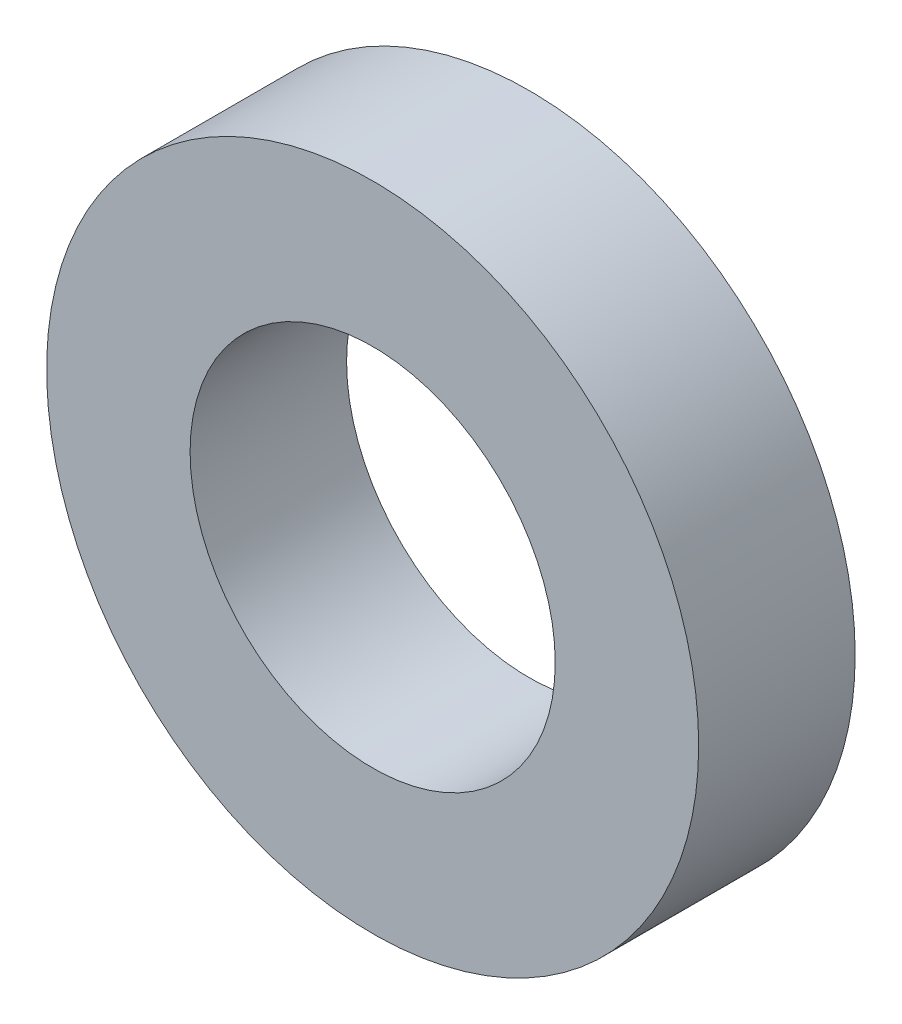
SolidWorks part; units mm, degrees
ref_plane "Front Plane" through (0, 0, 0) normal (0, 0, 1) x (1, 0, 0)
ref_plane "Top Plane" through (0, 0, 0) normal (0, 1, 0) x (1, 0, 0)
ref_plane "Right Plane" through (0, 0, 0) normal (1, 0, 0) x (0, 0, -1)
sketch "Sketch1" plane through (0, 0, 0) normal (0, 0, 1) x (1, 0, 0)
  circle A0 centre (0, 0) radius 7
  circle A1 centre (0, 0) radius 12.5
extrude "Boss-Extrude1" add sketch "Sketch1" along normal blind 6
